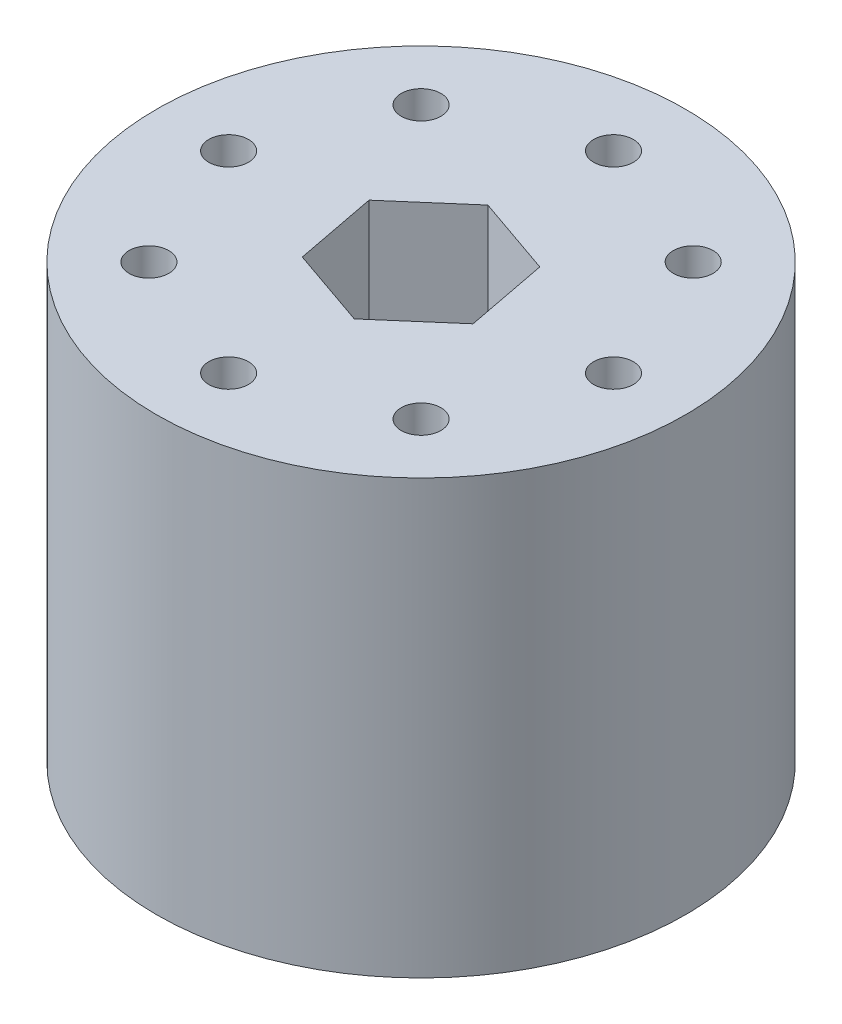
SolidWorks part; units mm, degrees
ref_plane "Front Plane" through (0, 0, 0) normal (0, 0, 1) x (1, 0, 0)
ref_plane "Top Plane" through (0, 0, 0) normal (0, 1, 0) x (1, 0, 0)
ref_plane "Right Plane" through (0, 0, 0) normal (1, 0, 0) x (0, 0, -1)
sketch "Sketch1" plane through (0, 0, 0) normal (0, 1, 0) x (1, 0, 0)
  circle A0 centre (0, 0) radius 22
extrude "Boss-Extrude1" add sketch "Sketch1" along normal blind 36
sketch "Sketch2" plane through (0, 36, 0) normal (0, 1, 0) x (1, 0, 0)
  line L0 (-11.3137, 11.3137) -> (11.3137, -11.3137) construction
  line L1 (11.3137, 11.3137) -> (-11.3137, -11.3137) construction
  line L2 (0, 16) -> (0, -16) construction
  line L3 (16, 0) -> (-16, 0) construction
  circle A3 centre (-11.3137, 11.3137) radius 1.65
  circle A4 centre (0, 16) radius 1.65
  circle A62 centre (16, 0) radius 1.65
  circle A63 centre (11.3137, 11.3137) radius 1.65
  circle A64 centre (0, -16) radius 1.65
  circle A65 centre (11.3137, -11.3137) radius 1.65
  circle A66 centre (-16, 0) radius 1.65
  circle A67 centre (-11.3137, -11.3137) radius 1.65
  circle A68 centre (-16, 0) radius 1.65 [skipped]
  circle A69 centre (-11.3137, -11.3137) radius 1.65 [skipped]
  circle A70 centre (0, -16) radius 1.65 [skipped]
  circle A71 centre (11.3137, -11.3137) radius 1.65 [skipped]
  circle A72 centre (16, 0) radius 1.65 [skipped]
  circle A73 centre (11.3137, 11.3137) radius 1.65 [skipped]
  point P0 (10.5837, 6.8291)
  point P1 (7.1476, -3.7464)
  point P25 (0, 0)
  point P43 (0, 0)
  point P172 (-1.004, 0.3293)
  dimension "D2" = 32
  dimension "D3" = 32
  dimension "D5" = 8
  dimension "D16" = 4
  dimension "D4" = 32
  dimension "D6" = 32
extrude "Cut-Extrude1" cut sketch "Sketch2" against normal up to vertex (36 mm away) up to point (0, 0, 0)
sketch "Sketch3" plane through (0, 36, 0) normal (0, 1, 0) x (1, 0, 0)
  line L1 (1.3217, -6.8741) -> (6.614, -2.2924)
  line L2 (6.614, -2.2924) -> (5.2923, 4.5817)
  line L3 (5.2923, 4.5817) -> (-1.3217, 6.8741)
  line L4 (-1.3217, 6.8741) -> (-6.614, 2.2924)
  line L5 (-6.614, 2.2924) -> (-5.2923, -4.5817)
  line L6 (-5.2923, -4.5817) -> (1.3217, -6.8741)
  circle A0 centre (0, 0) radius 6.0622 construction
  dimension "D1" = 7
extrude "Cut-Extrude2" cut sketch "Sketch3" against normal blind 10
sketch "Sketch4" plane through (0, 26, 0) normal (0, 1, 0) x (1, 0, 0)
  circle A0 centre (0, 0) radius 2.3
extrude "Cut-Extrude3" cut sketch "Sketch4" against normal blind 38
sketch "Sketch5" plane through (0, 0, 0) normal (0, -1, 0) x (-1, 0, 0)
  circle A0 centre (0, 0) radius 5.5954
extrude "Cut-Extrude4" cut sketch "Sketch5" against normal blind 9
